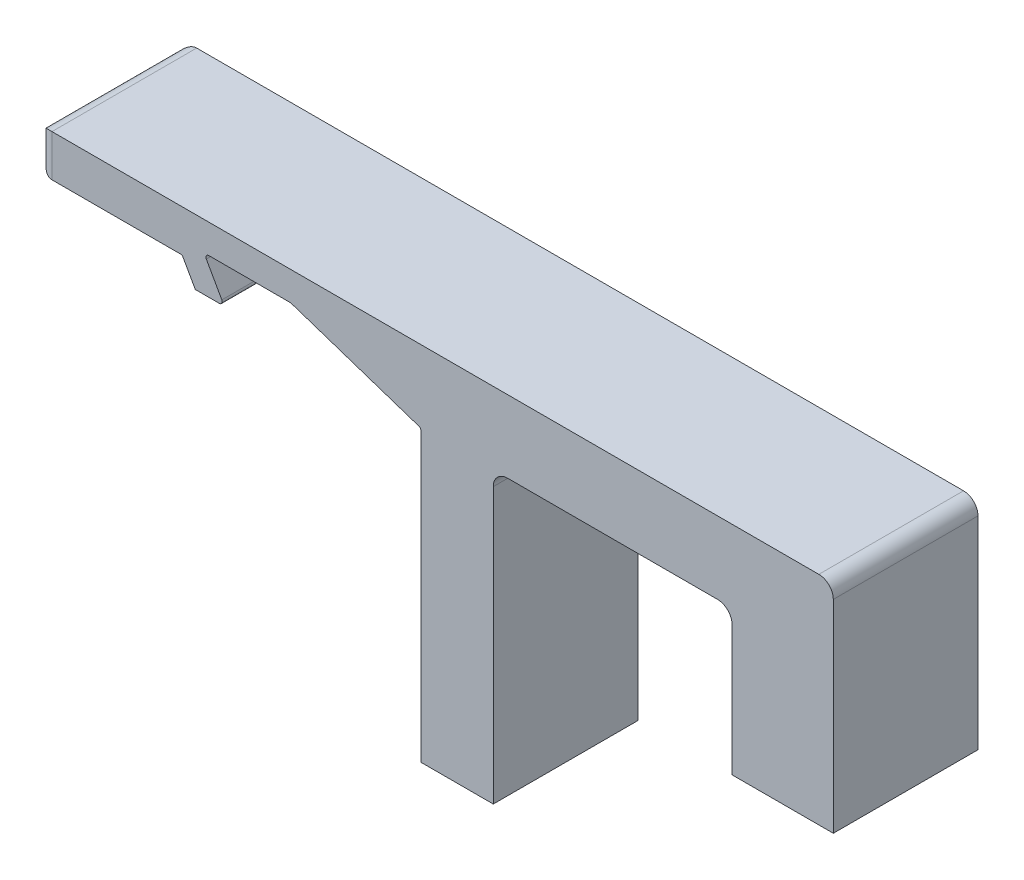
SolidWorks part; units mm, degrees
ref_plane "Front Plane" through (0, 0, 0) normal (0, 0, 1) x (1, 0, 0)
ref_plane "Top Plane" through (0, 0, 0) normal (0, 1, 0) x (1, 0, 0)
ref_plane "Right Plane" through (0, 0, 0) normal (1, 0, 0) x (0, 0, -1)
sketch "Sketch1" plane through (0, 0, 0) normal (0, 0, 1) x (1, 0, 0)
  line L1 (-48, 2.1115) -> (-48, 5)
  line L2 (-48, 5) -> (7, 5)
  line L3 (7, 5) -> (7, -10)
  line L4 (7, -10) -> (0, -10)
  line L5 (0, -10) -> (0, 0)
  line L6 (0, 0) -> (-16.5, 0)
  line L7 (-16.5, 0) -> (-16.5, -20)
  line L8 (-16.5, -20) -> (-21.5, -20)
  line L9 (-21.5, -20) -> (-21.5, 0)
  line L12 (-35.0931, 0.5) -> (-36.5, 3)
  line L14 (-48, 2.1115) -> (-38, 2.1115)
  line L16 (-36.5, 3) -> (-30.5, 3)
  line L17 (-38, 2.1115) -> (-37.0931, 0.5)
  line L18 (-37.0931, 0.5) -> (-35.0931, 0.5)
  line L19 (-30.5, 3) -> (-21.5, 0)
  dimension "D1" = 55
  dimension "D2" = 7
  dimension "D3" = 5
  dimension "D4" = 20
  dimension "D5" = 25
  dimension "D6" = 5
  dimension "D7" = 16.5
  dimension "D8" = 3
  dimension "D9" = 2
  dimension "D10" = 15
  dimension "D11" = 4.5
  dimension "D12" = 10
  dimension "D13" = 10
  dimension "D14" = 6
  dimension "D15" = 1.4069
extrude "Boss-Extrude1" add sketch "Sketch1" along normal blind 10
fillet "Fillet3" radius 0.2 5 edges at (-38, 2.1115, 5) (-35.0931, 0.5, 5) (-36.5, 3, 5) (-21.5, 0, 5) (-30.5, 3, 5)
fillet "Fillet4" radius 1 7 edges at (-48, 5, 5) (-48, 3.5558, 10) (-48, 2.1115, 5) (-48, 3.5558, 0) (7, 5, 5) (-16.5, 0, 5) (0, 0, 5)
